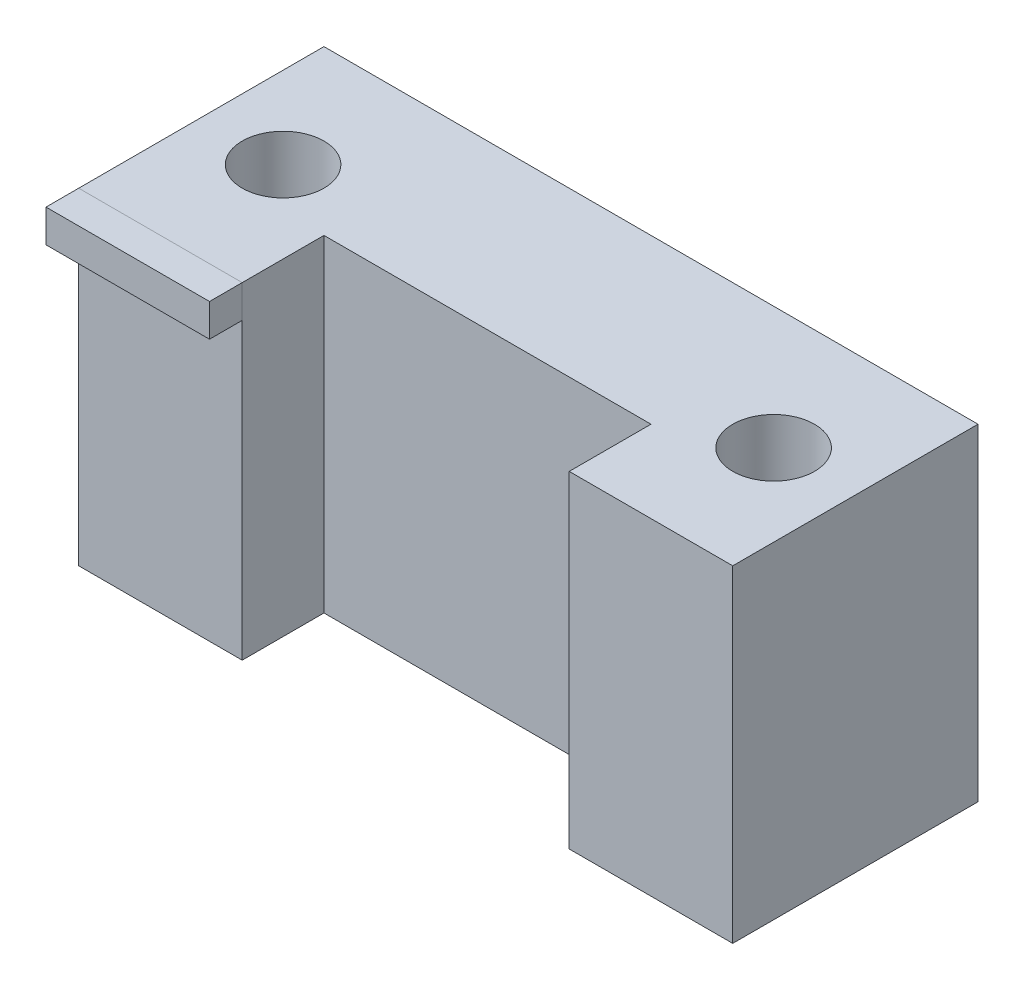
SolidWorks part; units mm, degrees
ref_plane "Front Plane" through (0, 0, 0) normal (0, 0, 1) x (1, 0, 0)
ref_plane "Top Plane" through (0, 0, 0) normal (0, 1, 0) x (1, 0, 0)
ref_plane "Right Plane" through (0, 0, 0) normal (1, 0, 0) x (0, 0, -1)
sketch "Sketch1" plane through (0, 0, 0) normal (0, 1, 0) x (1, 0, 0)
  line L0 (150, 0) -> (200, 0)
  line L1 (0, 0) -> (50, 0)
  line L2 (0, 0) -> (0, 75)
  line L3 (0, 75) -> (200, 75)
  line L4 (200, 0) -> (200, 75)
  line L6 (50, 0) -> (50, 25)
  line L7 (50, 25) -> (150, 25)
  line L8 (150, 0) -> (150, 25)
  line L9 (25, 37.5) -> (175, 37.5) construction
  point P9 (100, 25)
  point P10 (100, 75)
  point P13 (100, 37.5)
  point P14 (200, 37.5)
  dimension "D1" = 25
  dimension "D2" = 200
  dimension "D3" = 100
  dimension "D4" = 75
  dimension "D5" = 150
extrude "Boss-Extrude1" add sketch "Sketch1" along normal blind 100
hole_wizard "Hole1" positions "3DSketch2" profile "Sketch2" legacy end condition through all
sketch3d "3DSketch2"
  point P33 (175, 0, -37.5)
  point P39 (25, 0, -37.5)
sketch "Sketch2" plane through (175, 0, -37.5) normal (1, 0, 0) x (0, 0, -1)
  line L0 (0, 0) -> (0, 100)
  line L1 (0, 100) -> (12.5, 100)
  line L2 (12.5, 100) -> (12.5, 0)
  line L3 (12.5, 0) -> (0, 0)
  line L4 (0, 110) -> (0, -10) construction
  dimension "Diameter" = 25
  dimension "Depth" = 100
sketch "Sketch3" plane through (0, 0, 0) normal (0, 0, 1) x (1, 0, 0)
  line L1 (0, 100) -> (50, 100)
  line L2 (0, 100) -> (0, 90)
  line L3 (0, 90) -> (50, 90)
  line L4 (50, 100) -> (50, 90)
  dimension "D1" = 50
  dimension "10" = 10
extrude "Boss-Extrude2" add sketch "Sketch3" along normal blind 10 separate body
